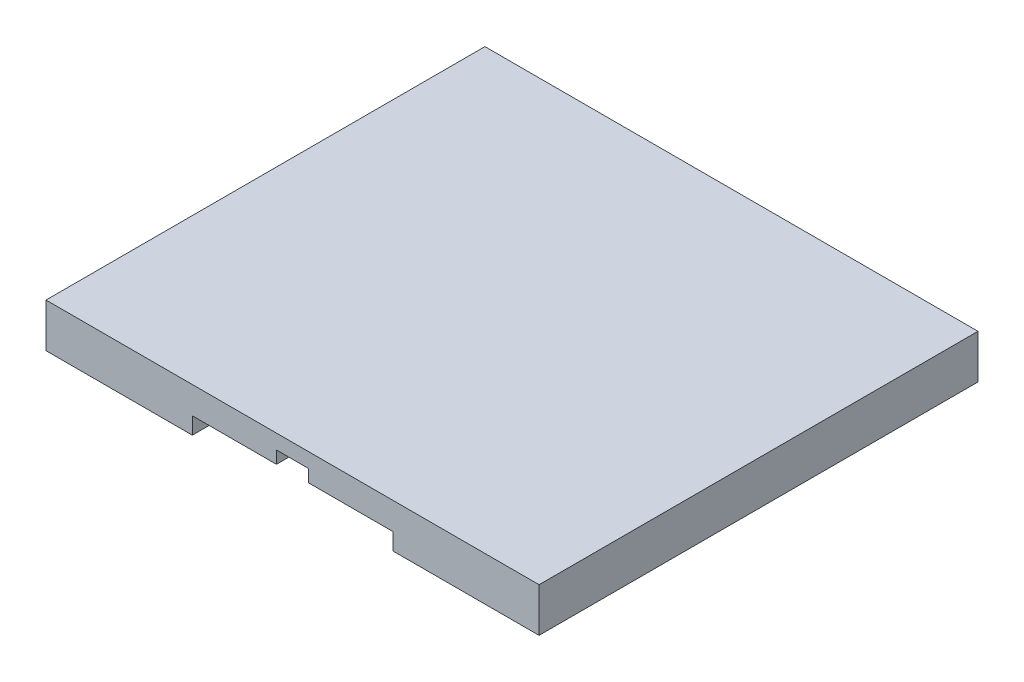
SolidWorks part; units mm, degrees
ref_plane "Front Plane" through (0, 0, 0) normal (0, 0, 1) x (1, 0, 0)
ref_plane "Top Plane" through (0, 0, 0) normal (0, 1, 0) x (1, 0, 0)
ref_plane "Right Plane" through (0, 0, 0) normal (1, 0, 0) x (0, 0, -1)
ref_plane "Plane1" through (0, 30, 0) normal (0, 1, 0) x (1, 0, 0)
sketch "Sketch5" plane through (0, 0, 0) normal (0, 1, 0) x (1, 0, 0)
  line L0 (100, 199) -> (100, 300)
  line L1 (0, 0) -> (100, 0)
  line L2 (0, 0) -> (0, 300)
  line L3 (0, 300) -> (100, 300)
  line L4 (100, 0) -> (100, 101)
  line L5 (237, 0) -> (337, 0)
  line L6 (237, 0) -> (237, 101)
  line L7 (237, 300) -> (337, 300)
  line L8 (337, 0) -> (337, 300)
  line L9 (100, 199) -> (237, 199)
  line L11 (100, 101) -> (237, 101)
  line L13 (237, 199) -> (237, 300)
extrude "Boss-Extrude3" add sketch "Sketch5" along normal up to surface (30 mm away) up to plane "Plane1"
sketch "Sketch8" plane through (0, 30, 0) normal (0, 1, 0) x (1, 0, 0)
  line L0 (237, 0) -> (337, 0) construction
  line L1 (100, 300) -> (237, 300)
  line L2 (100, 300) -> (100, 199)
  line L3 (100, 199) -> (237, 199)
  line L4 (237, 300) -> (237, 199)
  line L5 (100, 101) -> (237, 101)
  line L6 (100, 101) -> (100, 0)
  line L7 (100, 0) -> (237, 0)
  line L8 (237, 101) -> (237, 0)
  line L9 (237, 101) -> (237, 0) construction
extrude "Boss-Extrude5" add sketch "Sketch8" against normal blind 10
sketch "Sketch9" plane through (0, 20, 0) normal (0, 1, 0) x (1, 0, 0)
  line L0 (0, 0) -> (337, 0) construction
  line L1 (100, 0) -> (157.5, 0)
  line L2 (100, 0) -> (100, 101)
  line L3 (100, 101) -> (157.5, 101)
  line L4 (157.5, 0) -> (157.5, 101)
  line L6 (179.5, 0) -> (237, 0)
  line L7 (179.5, 0) -> (179.5, 101)
  line L8 (179.5, 101) -> (237, 101)
  line L9 (237, 0) -> (237, 101)
sketch "Sketch10" plane through (0, 20, 0) normal (0, 1, 0) x (1, 0, 0)
  line L1 (100, 199) -> (157.5, 199)
  line L2 (100, 199) -> (100, 300)
  line L3 (100, 300) -> (157.5, 300)
  line L4 (157.5, 199) -> (157.5, 300)
  line L6 (179, 199) -> (237, 199)
  line L7 (179, 199) -> (179, 300)
  line L8 (179, 300) -> (237, 300)
  line L9 (237, 199) -> (237, 300)
extrude "Boss-Extrude6" add sketch "Sketch9" against normal blind 8.5
extrude "Boss-Extrude7" add sketch "Sketch10" against normal blind 8.5
sketch "Sketch13" plane through (0, 11.5, 0) normal (0, -1, 0) x (1, 0, 0)
  circle A0 centre (147.5, -8.5) radius 2.5
  circle A7 centre (147.5, -92.5) radius 2.5
  circle A8 centre (147.5, -80.5) radius 2.5 [skipped]
  circle A9 centre (147.5, -20.5) radius 2.5 [skipped]
  circle A10 centre (147.5, -68.5) radius 2.5 [skipped]
  circle A11 centre (147.5, -32.5) radius 2.5 [skipped]
  circle A12 centre (147.5, -44.5) radius 2.5 [skipped]
  circle A13 centre (147.5, -56.5) radius 2.5 [skipped]
  dimension "D1" = 8
sketch "Sketch14" plane through (0, 11.5, 0) normal (0, -1, 0) x (1, 0, 0)
  circle A0 centre (189.5, -8.5) radius 2.5
  circle A7 centre (189.5, -92.5) radius 2.5
  circle A8 centre (189.5, -20.5) radius 2.5 [skipped]
  circle A9 centre (189.5, -32.5) radius 2.5 [skipped]
  circle A10 centre (189.5, -44.5) radius 2.5 [skipped]
  circle A11 centre (189.5, -56.5) radius 2.5 [skipped]
  circle A12 centre (189.5, -68.5) radius 2.5 [skipped]
  circle A13 centre (189.5, -80.5) radius 2.5 [skipped]
  dimension "D1" = 8
sketch "Sketch15" plane through (0, 11.5, 0) normal (0, -1, 0) x (1, 0, 0)
  circle A0 centre (147.5, -207.5) radius 2.5
  circle A7 centre (147.5, -291.5) radius 2.5
  circle A8 centre (147.5, -279.5) radius 2.5 [skipped]
  circle A9 centre (147.5, -267.5) radius 2.5 [skipped]
  circle A10 centre (147.5, -255.5) radius 2.5 [skipped]
  circle A11 centre (147.5, -243.5) radius 2.5 [skipped]
  circle A12 centre (147.5, -219.5) radius 2.5 [skipped]
  circle A13 centre (147.5, -231.5) radius 2.5 [skipped]
  dimension "D1" = 8
sketch "Sketch16" plane through (0, 11.5, 0) normal (0, -1, 0) x (1, 0, 0)
  circle A0 centre (189.5, -207.5) radius 2.5
  circle A7 centre (189.5, -291.5) radius 2.5
  circle A8 centre (189.5, -219.5) radius 2.5 [skipped]
  circle A9 centre (189.5, -231.5) radius 2.5 [skipped]
  circle A10 centre (189.5, -243.5) radius 2.5 [skipped]
  circle A11 centre (189.5, -255.5) radius 2.5 [skipped]
  circle A12 centre (189.5, -267.5) radius 2.5 [skipped]
  circle A13 centre (189.5, -279.5) radius 2.5 [skipped]
  dimension "D1" = 8
extrude "Cut-Extrude1" cut sketch "Sketch13" against normal blind 8
extrude "Cut-Extrude2" cut sketch "Sketch14" against normal blind 8
extrude "Cut-Extrude3" cut sketch "Sketch15" against normal blind 8
extrude "Cut-Extrude4" cut sketch "Sketch16" against normal blind 8
